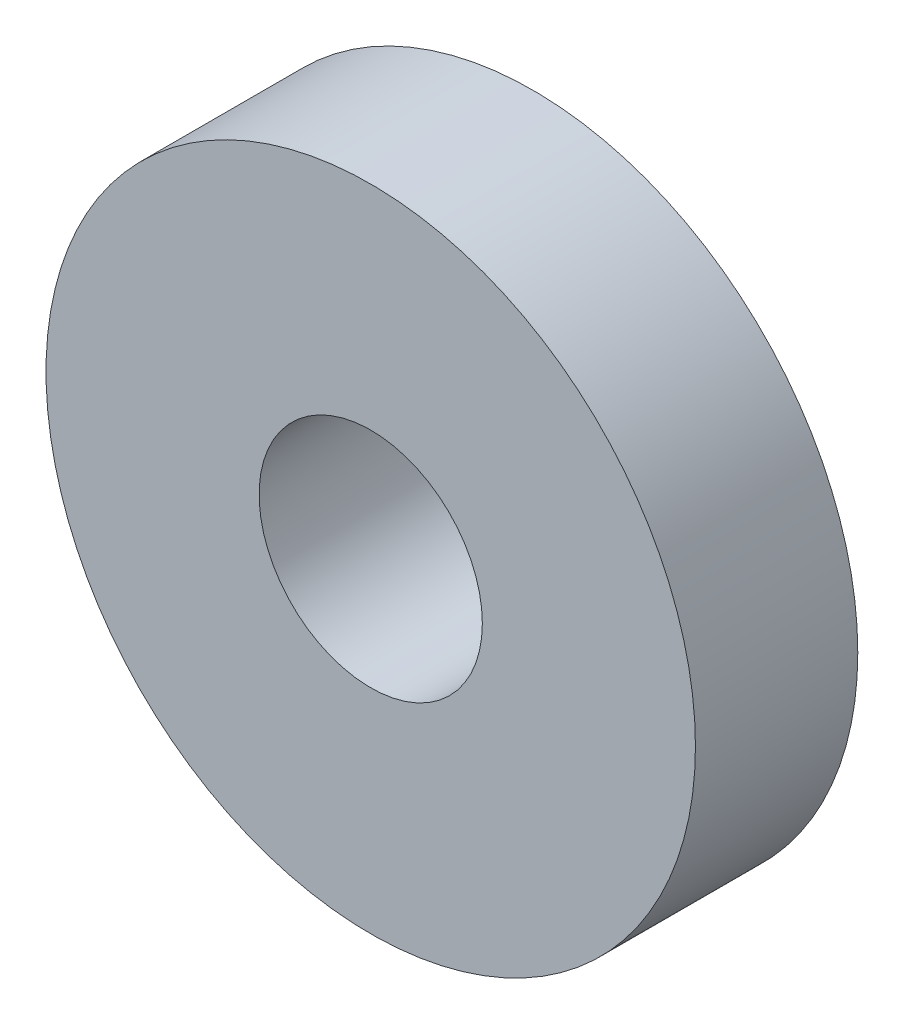
SolidWorks part; units mm, degrees
ref_plane "Płaszczyzna przednia" through (0, 0, 0) normal (0, 0, 1) x (1, 0, 0)
ref_plane "Płaszczyzna górna" through (0, 0, 0) normal (0, 1, 0) x (1, 0, 0)
ref_plane "Płaszczyzna prawa" through (0, 0, 0) normal (1, 0, 0) x (0, 0, -1)
sketch "Sketch1" plane through (0, 0, 0) normal (0, 0, 1) x (1, 0, 0)
  circle A2 centre (0, 0) radius 3.2
  circle A3 centre (0, 0) radius 1.1
  dimension "D1" = 2.2
  dimension "D2" = 6.4
extrude "Boss-Extrude1" add sketch "Sketch1" along normal blind 1.6
